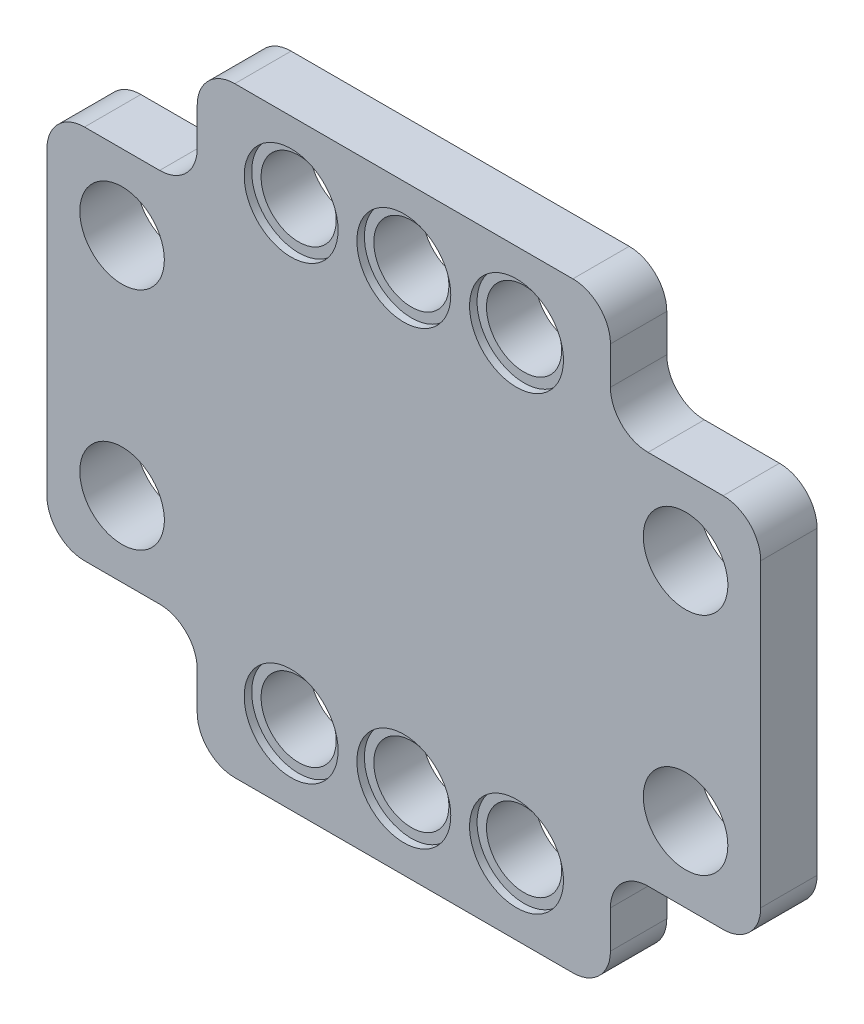
SolidWorks part; units mm, degrees
ref_plane "Plan de face" through (0, 0, 0) normal (0, 0, 1) x (1, 0, 0)
ref_plane "Plan de dessus" through (0, 0, 0) normal (0, 1, 0) x (1, 0, 0)
ref_plane "Plan de droite" through (0, 0, 0) normal (1, 0, 0) x (0, 0, -1)
sketch "Esquisse2" plane through (0, 0, 0) normal (0, 0, 1) x (1, 0, 0)
  line L1 (0, 0) -> (38, 0)
  line L2 (0, 0) -> (0, 32)
  line L3 (0, 32) -> (38, 32)
  line L4 (38, 0) -> (38, 32)
  dimension "D1" = 38
  dimension "D2" = 32
extrude "Boss.-Extru.1" add sketch "Esquisse2" along normal blind 3
sketch "Esquisse3" plane through (0, 0, 3) normal (0, 0, 1) x (1, 0, 0)
  line L0 (19, 0) -> (19, 32) construction
  line L1 (0, 0) -> (38, 0) construction
  line L2 (38, 32) -> (0, 32) construction
  line L3 (0, 16) -> (38, 16) construction
  line L4 (0, 32) -> (0, 0) construction
  line L5 (38, 0) -> (38, 32) construction
  line L6 (13, 28) -> (19, 28) construction
  line L7 (13, 4) -> (19, 4) construction
  circle A0 centre (19, 28) radius 2
  circle A1 centre (13, 28) radius 2
  circle A2 centre (25, 28) radius 2
  circle A3 centre (25, 4) radius 2
  circle A4 centre (13, 4) radius 2
  circle A5 centre (19, 4) radius 2
  circle A6 centre (4, 22) radius 2.25
  circle A7 centre (4, 10) radius 2.25
  circle A8 centre (34, 10) radius 2.25
  circle A9 centre (34, 22) radius 2.25
  dimension "D1" = 4
  dimension "D2" = 24
  dimension "D3" = 6
  dimension "D4" = 4.5
  dimension "D5" = 12
  dimension "D6" = 30
extrude "Enlèv. mat.-Extru.1" cut sketch "Esquisse3" against normal through all both and the other way through all
sketch "Esquisse4" plane through (0, 0, 3) normal (0, 0, 1) x (1, 0, 0)
  circle A0 centre (13, 4) radius 2.5
  circle A1 centre (19, 4) radius 2.5
  circle A2 centre (25, 4) radius 2.5
  circle A3 centre (25, 28) radius 2.5
  circle A4 centre (19, 28) radius 2.5
  circle A5 centre (13, 28) radius 2.5
  dimension "D1" = 5
extrude "Enlèv. mat.-Extru.2" cut sketch "Esquisse4" against normal blind 0.4
sketch "Esquisse5" plane through (0, 0, 3) normal (0, 0, 1) x (1, 0, 0)
  line L0 (19, 32) -> (19, 0) construction
  line L1 (0, 32) -> (8, 32)
  line L2 (0, 32) -> (0, 26)
  line L3 (0, 26) -> (8, 26)
  line L4 (8, 32) -> (8, 26)
  line L5 (38, 32) -> (0, 32) construction
  line L6 (0, 0) -> (38, 0) construction
  line L7 (38, 16) -> (0, 16) construction
  line L8 (38, 0) -> (38, 32) construction
  line L9 (0, 32) -> (0, 0) construction
  line L10 (30, 32) -> (30, 26)
  line L11 (38, 26) -> (30, 26)
  line L12 (38, 32) -> (38, 26)
  line L13 (38, 32) -> (30, 32)
  line L14 (38, 0) -> (30, 0)
  line L15 (38, 0) -> (38, 6)
  line L16 (38, 6) -> (30, 6)
  line L17 (30, 0) -> (30, 6)
  line L18 (8, 0) -> (8, 6)
  line L19 (0, 6) -> (8, 6)
  line L20 (0, 0) -> (0, 6)
  line L21 (0, 0) -> (8, 0)
  dimension "D1" = 6
  dimension "D2" = 8
extrude "Enlèv. mat.-Extru.3" cut sketch "Esquisse5" against normal through all both and the other way through all
fillet "Congé1" radius 2 12 edges at (30, 32, 1.5) (30, 26, 1.5) (38, 26, 1.5) (38, 6, 1.5) (30, 6, 1.5) (30, 0, 1.5) (8, 0, 1.5) (8, 6, 1.5) (0, 6, 1.5) (0, 26, 1.5) (8, 32, 1.5) (8, 26, 1.5)
